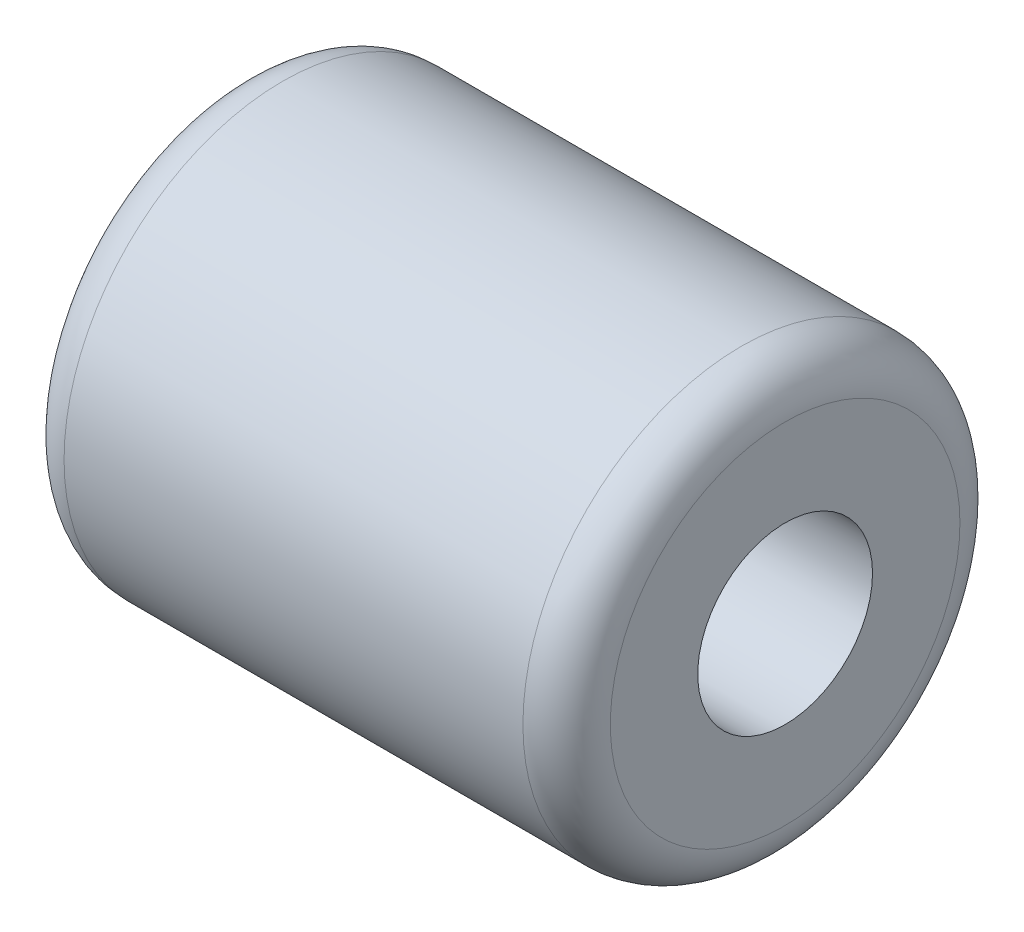
SolidWorks part; units mm, degrees
ref_plane "Front Plane" through (0, 0, 0) normal (0, 0, 1) x (1, 0, 0)
ref_plane "Top Plane" through (0, 0, 0) normal (0, 1, 0) x (1, 0, 0)
ref_plane "Right Plane" through (0, 0, 0) normal (1, 0, 0) x (0, 0, -1)
sketch "Sketch1" plane through (0, 0, 0) normal (1, 0, 0) x (0, 0, -1)
  circle A0 centre (0, 0) radius 10
  dimension "D1" = 20
extrude "Boss-Extrude1" add sketch "Sketch1" along normal blind 25
sketch "Sketch2" plane through (25, 0, 0) normal (1, 0, 0) x (0, 0, -1)
  circle A0 centre (0, 0) radius 4
  dimension "D1" = 8
extrude "Cut-Extrude1" cut sketch "Sketch2" against normal through all
fillet "Fillet1" radius 2 2 edges at (25, 0, -10) (0, 0, -10)
